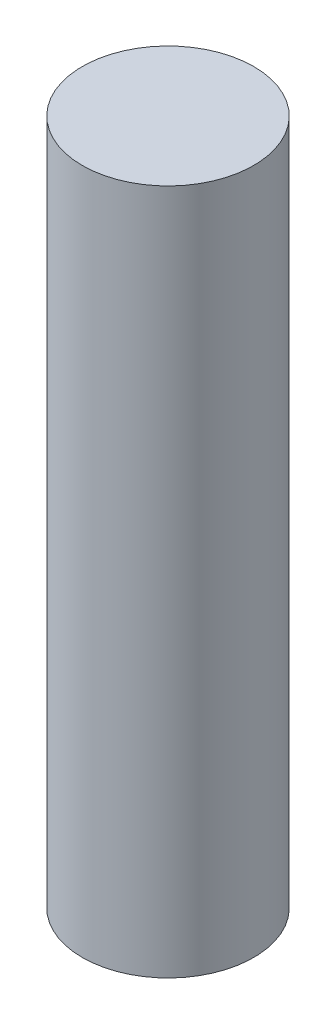
SolidWorks part; units mm, degrees
ref_plane "Alzado" through (0, 0, 0) normal (0, 0, 1) x (1, 0, 0)
ref_plane "Planta" through (0, 0, 0) normal (0, 1, 0) x (1, 0, 0)
ref_plane "Vista lateral" through (0, 0, 0) normal (1, 0, 0) x (0, 0, -1)
sketch "Croquis1" plane through (0, 0, 0) normal (0, 1, 0) x (1, 0, 0)
  circle A0 centre (0, 0) radius 7.5
  dimension "D1" = 15
extrude "Saliente-Extruir1" add sketch "Croquis1" along normal blind 60
